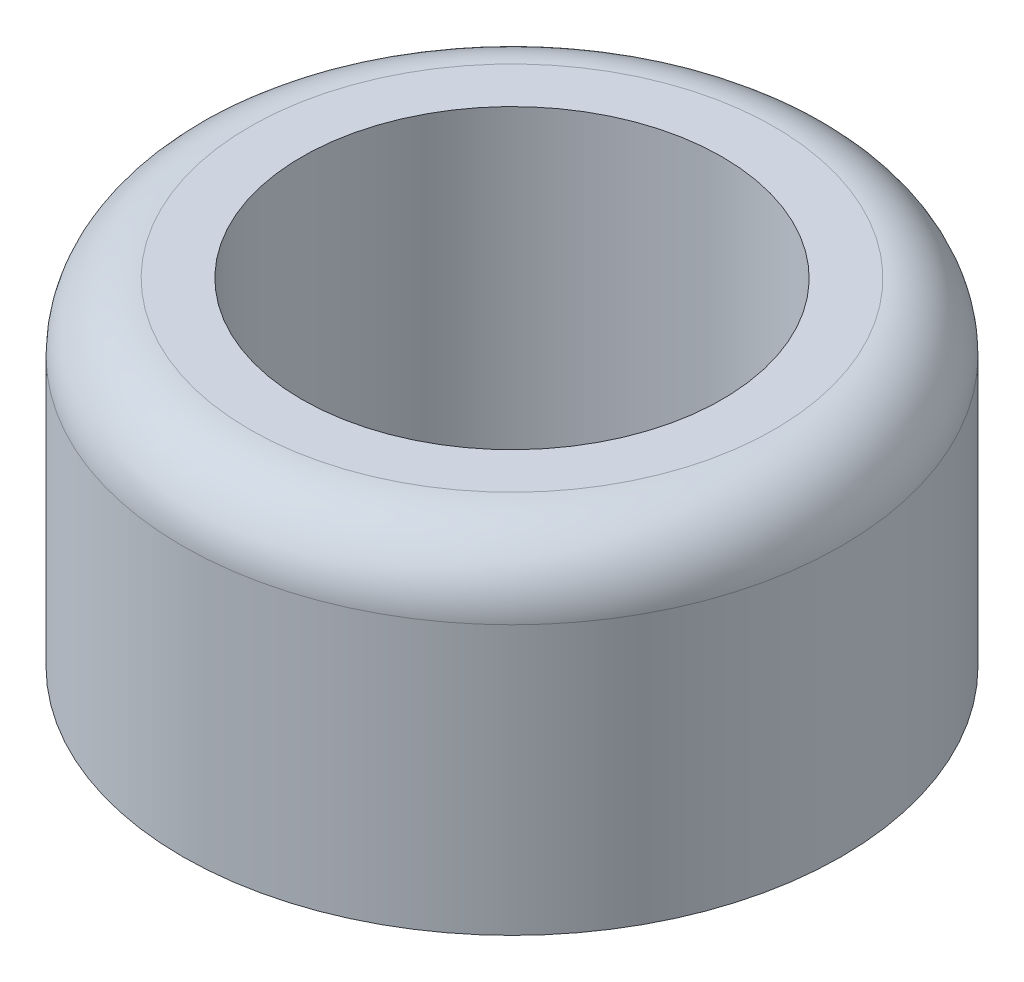
SolidWorks part; units mm, degrees
ref_plane "Front Plane" through (0, 0, 0) normal (0, 0, 1) x (1, 0, 0)
ref_plane "Top Plane" through (0, 0, 0) normal (0, 1, 0) x (1, 0, 0)
ref_plane "Right Plane" through (0, 0, 0) normal (1, 0, 0) x (0, 0, -1)
sketch "Sketch1" plane through (0, 0, 0) normal (0, 1, 0) x (1, 0, 0)
  circle A0 centre (0, 0) radius 4.9
  circle A1 centre (0, 0) radius 3.125
  dimension "D1" = 6.25
  dimension "D2" = 9.8
extrude "Boss-Extrude1" add sketch "Sketch1" along normal blind 5
fillet "Fillet1" radius 1 1 edges at (0, 5, 4.9)
